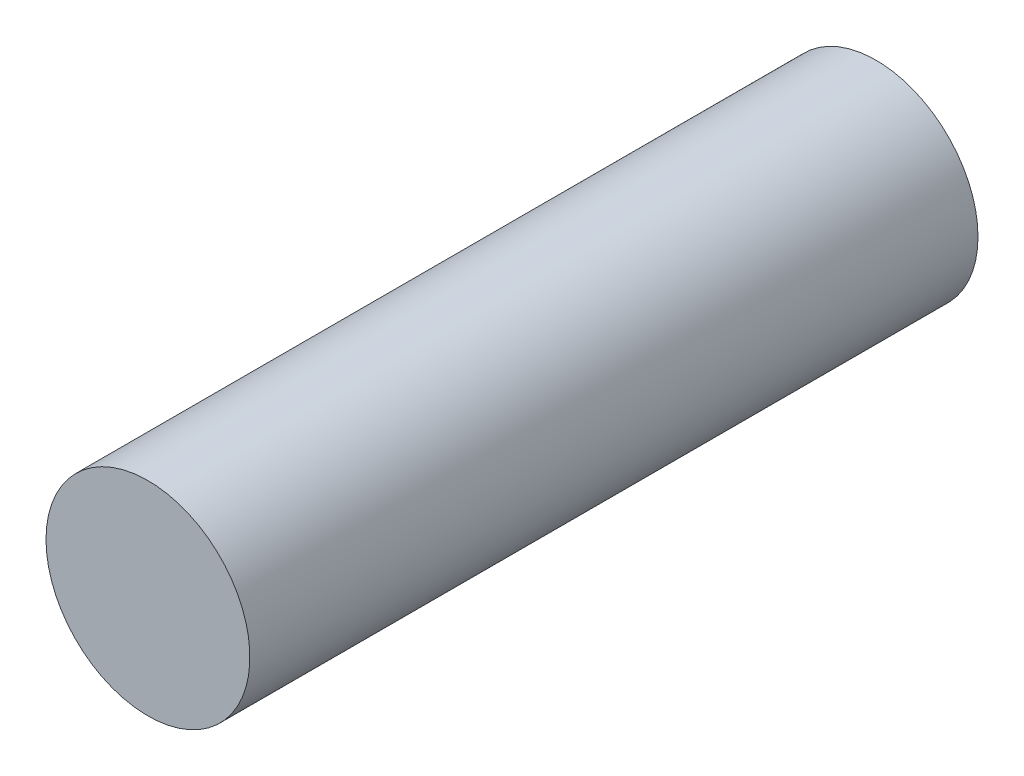
SolidWorks part; units mm, degrees
ref_plane "Front Plane" through (0, 0, 0) normal (0, 0, 1) x (1, 0, 0)
ref_plane "Top Plane" through (0, 0, 0) normal (0, 1, 0) x (1, 0, 0)
ref_plane "Right Plane" through (0, 0, 0) normal (1, 0, 0) x (0, 0, -1)
sketch "Sketch2" plane through (0, 0, 0) normal (0, 0, 1) x (1, 0, 0)
  line L0 (-1.2374, -1.2374) -> (1.2374, -1.2374)
  arc A0 (1.2374, -1.2374) -> (-1.2374, -1.2374) centre (0, 0) ccw
  circle A1 centre (0, 0) radius 3.5
  dimension "D1" = 3.5
  dimension "D2" = 7
extrude "Boss-Extrude1" add sketch "Sketch2" along normal blind 8
sketch "Sketch3" plane through (0, 0, 8) normal (0, 0, 1) x (1, 0, 0)
  circle A0 centre (0, 0) radius 3.5
extrude "Boss-Extrude2" add sketch "Sketch3" along normal blind 18
sketch "Sketch4" plane through (0, 0, 26) normal (0, 0, 1) x (1, 0, 0)
  line L0 (-6.25, -4) -> (-6.25, 4)
  line L1 (-4.25, -2) -> (4.25, -2)
  line L2 (-4.25, -2) -> (-4.25, 2)
  line L3 (-4.25, 2) -> (4.25, 2)
  line L4 (4.25, -2) -> (4.25, 2)
  line L5 (-4.25, -2) -> (4.25, 2) construction
  line L6 (-4.25, 2) -> (4.25, -2) construction
  line L7 (-6.25, 4) -> (6.25, 4)
  line L8 (6.25, -4) -> (6.25, 4)
  line L9 (-6.25, -4) -> (6.25, -4)
  point P0 (0, 0)
  dimension "D1" = 8.5
  dimension "D2" = 4
  dimension "D3" = 2
extrude "Boss-Extrude3" add sketch "Sketch4" along normal blind 10
sketch "Sketch5" plane through (0, 0, 26) normal (0, 0, -1) x (-1, 0, 0)
  line L1 (6.25, 4) -> (-6.25, 4)
  line L2 (6.25, 4) -> (6.25, -4)
  line L3 (6.25, -4) -> (-6.25, -4)
  line L4 (-6.25, 4) -> (-6.25, -4)
extrude "Boss-Extrude4" add sketch "Sketch5" along normal blind 1
fillet "Fillet2" radius 2 4 edges at (6.25, 4, 30.5) (-6.25, -4, 30.5) (6.25, -4, 30.5) (-6.25, 4, 30.5)
sketch "Sketch6" plane through (0, 0, 25) normal (0, 0, -1) x (-1, 0, 0)
  line L1 (-8.1674, 4.3797) -> (7.2097, 4.3797)
  line L2 (-8.1674, 4.3797) -> (-8.1674, -4.9208)
  line L3 (-8.1674, -4.9208) -> (7.2097, -4.9208)
  line L4 (7.2097, 4.3797) -> (7.2097, -4.9208)
extrude "Cut-Extrude1" cut sketch "Sketch6" against normal through all
